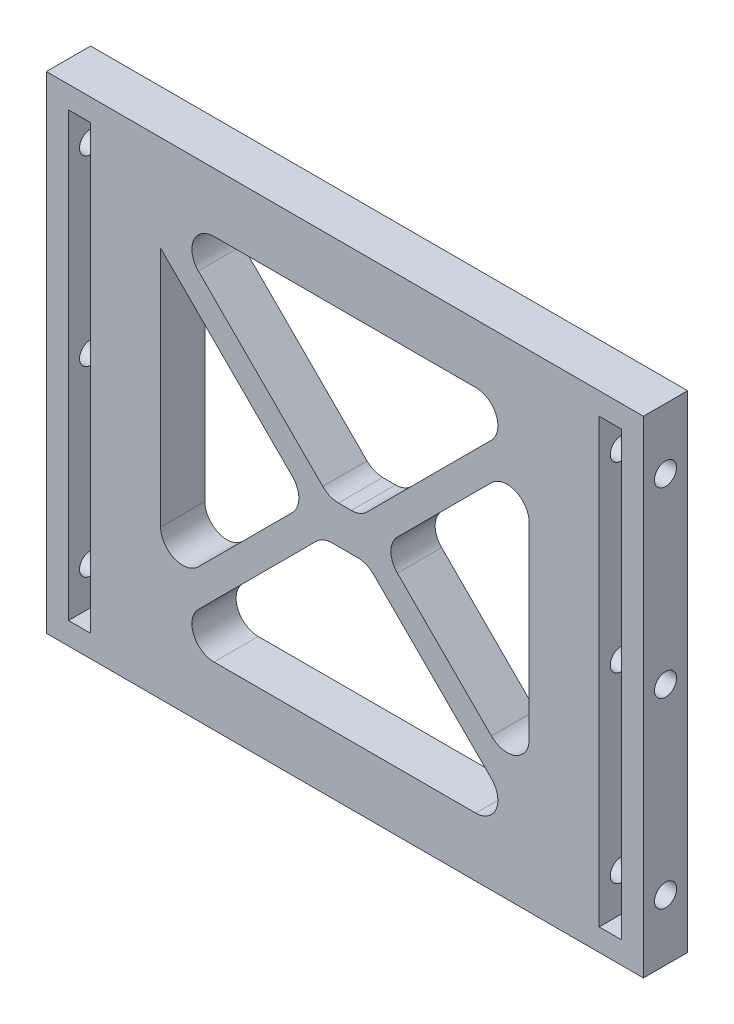
SolidWorks part; units mm, degrees
material "6061 Alloy"
ref_plane "Front Plane" through (0, 0, 0) normal (0, 0, 1) x (1, 0, 0)
ref_plane "Top Plane" through (0, 0, 0) normal (0, 1, 0) x (1, 0, 0)
ref_plane "Right Plane" through (0, 0, 0) normal (1, 0, 0) x (0, 0, -1)
sketch "Sketch1" plane through (0, 0, 0) normal (0, 0, 1) x (1, 0, 0)
  line L1 (40.5, -33) -> (-40.5, -33)
  line L2 (40.5, -33) -> (40.5, 33)
  line L3 (40.5, 33) -> (-40.5, 33)
  line L4 (-40.5, -33) -> (-40.5, 33)
  line L5 (40.5, -33) -> (-40.5, 33) construction
  line L6 (40.5, 33) -> (-40.5, -33) construction
  point P0 (0, 0)
  dimension "D1" = 81
  dimension "D2" = 66
extrude "Boss-Extrude1" add sketch "Sketch1" along normal blind 6
sketch "Sketch3" plane through (0, 0, 6) normal (0, 0, 1) x (1, 0, 0)
  line L0 (-40.5, 33) -> (-40.5, -33) construction
  line L1 (37.5, -30) -> (-37.5, -30)
  line L2 (37.5, -30) -> (37.5, 30)
  line L3 (37.5, 30) -> (-37.5, 30)
  line L4 (-37.5, -30) -> (-37.5, 30)
  line L5 (37.5, -30) -> (-37.5, 30) construction
  line L6 (37.5, 30) -> (-37.5, -30) construction
  line L7 (40.5, 33) -> (-40.5, 33) construction
  line L9 (-34.5, 30) -> (-34.5, -30)
  line L10 (34.5, 30) -> (34.5, -30)
  point P0 (0, 0)
  dimension "D1" = 3
  dimension "D2" = 3
  dimension "D3" = 3
  dimension "D4" = 3
extrude "Cut-Extrude2" cut sketch "Sketch3" against normal through all contours L9 L3 L4 L1 | L3 L10 L1 L2
sketch "Sketch5" plane through (0, 0, 6) normal (0, 0, 1) x (1, 0, 0)
  line L0 (-25, 20) -> (-5, 0)
  line L1 (25, -25) -> (-25, -25)
  line L2 (25, -25) -> (25, 25)
  line L3 (25, 25) -> (-25, 25)
  line L4 (-25, -25) -> (-25, 25)
  line L5 (25, -25) -> (-25, 25) construction
  line L6 (25, 25) -> (-25, -25) construction
  line L7 (-5, 0) -> (-25, -20)
  line L8 (-25, 25) -> (0, 0)
  line L9 (0, 0) -> (-25, -25)
  line L10 (-25, -25) -> (0, 0)
  line L11 (-25, 25) -> (0, 0)
  line L12 (0, 25) -> (0, -25)
  line L13 (5, 0) -> (25, -20)
  line L14 (0, 0) -> (25, -25)
  line L15 (25, 25) -> (0, 0)
  line L16 (25, 20) -> (5, 0)
  line L17 (-2.1213, 2.1213) -> (2.1213, 2.1213)
  line L21 (-3, -3) -> (3, -3)
  line L22 (0, 0) -> (3, -3)
  point P0 (0, 0)
  dimension "D1" = 50
  dimension "D2" = 50
  dimension "D3" = 5
  dimension "D4" = 5
  dimension "D5" = 3
  dimension "D6" = 3
extrude "Cut-Extrude5" cut sketch "Sketch5" against normal through all contours L7 L0 L4 | L21 L10 L1 L12 | L21 L12 L1 L14 | L2 L16 L13 | L12 L17 L15 L3 | L8 L17 L12 L3
fillet "Fillet2" radius 3 7 edges at (-25, 25, 3) (-25, -20, 3) (-25, -25, 3) (25, -25, 3) (25, -20, 3) (25, 20, 3) (25, 25, 3)
fillet "Fillet3" radius 3 6 edges at (-5, 0, 3) (-3, -3, 3) (3, -3, 3) (5, 0, 3) (-2.1213, 2.1213, 3) (2.1213, 2.1213, 3)
sketch "Sketch6" plane through (-40.5, 0, 0) normal (-1, 0, 0) x (0, 0, 1)
  line L0 (3, 33) -> (3, -33) construction
  line L1 (6, 33) -> (0, 33) construction
  line L2 (6, -33) -> (0, -33) construction
  line L3 (3, 0) -> (3, 33) construction
  line L4 (3, 16.5) -> (3, 33) construction
  line L5 (0, 0) -> (6, 0) construction
  line L6 (6, 33) -> (6, -33) construction
  circle A0 centre (3, 24.75) radius 1.5
  circle A1 centre (3, 0) radius 1.5
  circle A2 centre (3, -24.75) radius 1.5
extrude "Cut-Extrude6" cut sketch "Sketch6" against normal blind 10
mirror "Mirror1" about plane through (0, 0, 0) normal (1, 0, 0) of "Cut-Extrude6"
